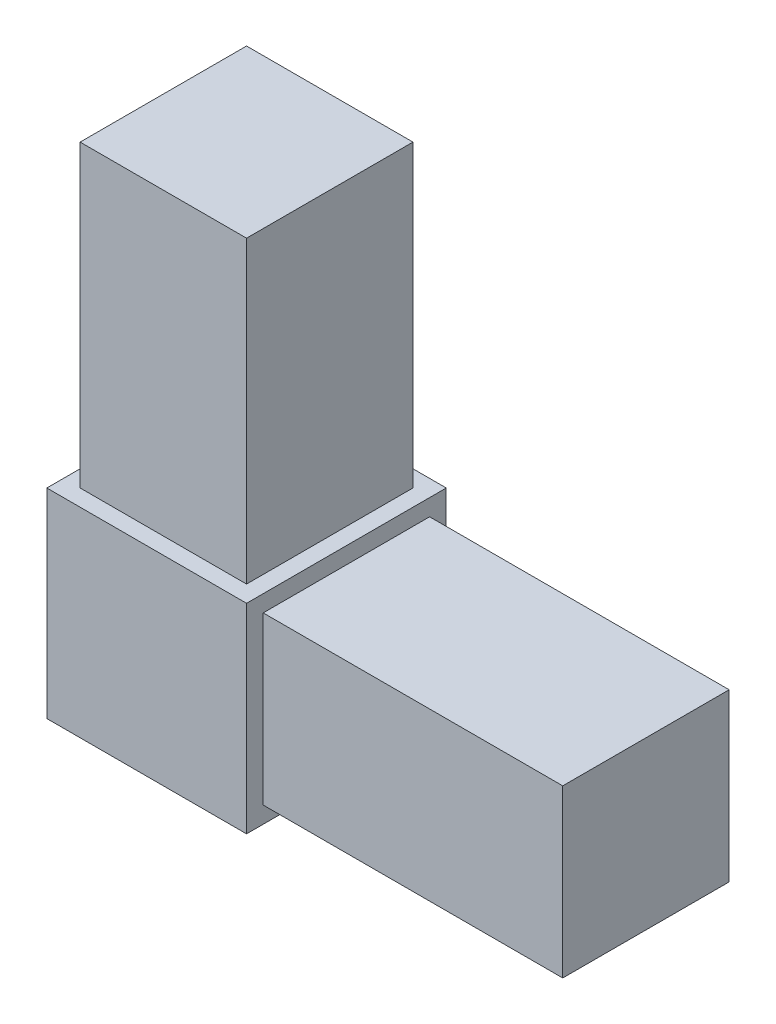
SolidWorks part; units mm, degrees
material "ABS"
ref_plane "Front Plane" through (0, 0, 0) normal (0, 0, 1) x (1, 0, 0)
ref_plane "Top Plane" through (0, 0, 0) normal (0, 1, 0) x (1, 0, 0)
ref_plane "Right Plane" through (0, 0, 0) normal (1, 0, 0) x (0, 0, -1)
sketch "Sketch1" plane through (0, 0, 0) normal (0, 0, 1) x (1, 0, 0)
  line L1 (9.525, -9.525) -> (-9.525, -9.525)
  line L2 (9.525, -9.525) -> (9.525, 9.525)
  line L3 (9.525, 9.525) -> (-9.525, 9.525)
  line L4 (-9.525, -9.525) -> (-9.525, 9.525)
  line L5 (9.525, -9.525) -> (-9.525, 9.525) construction
  line L6 (9.525, 9.525) -> (-9.525, -9.525) construction
  point P0 (0, 0)
  dimension "D1" = 19.05
extrude "Boss-Extrude1" add sketch "Sketch1" along normal blind 19.05
sketch "Sketch2" plane through (0, 9.525, 0) normal (0, 1, 0) x (1, 0, 0)
  line L0 (-9.525, 0) -> (9.525, -19.05) construction
  line L2 (-7.9375, -1.5875) -> (7.9375, -1.5875)
  line L3 (-7.9375, -1.5875) -> (-7.9375, -17.4625)
  line L4 (-7.9375, -17.4625) -> (7.9375, -17.4625)
  line L5 (7.9375, -1.5875) -> (7.9375, -17.4625)
  line L6 (-7.9375, -1.5875) -> (7.9375, -17.4625) construction
  line L7 (-7.9375, -17.4625) -> (7.9375, -1.5875) construction
  point P4 (0, -9.525)
  dimension "D1" = 15.875
extrude "Boss-Extrude2" add sketch "Sketch2" along normal blind 28.575
sketch "Sketch3" plane through (9.525, 0, 0) normal (1, 0, 0) x (0, 0, -1)
  line L0 (-19.05, 9.525) -> (0, -9.525) construction
  line L2 (-17.4625, -7.9375) -> (-1.5875, -7.9375)
  line L3 (-17.4625, -7.9375) -> (-17.4625, 7.9375)
  line L4 (-17.4625, 7.9375) -> (-1.5875, 7.9375)
  line L5 (-1.5875, -7.9375) -> (-1.5875, 7.9375)
  line L6 (-17.4625, -7.9375) -> (-1.5875, 7.9375) construction
  line L7 (-17.4625, 7.9375) -> (-1.5875, -7.9375) construction
  point P4 (-9.525, 0)
  dimension "D1" = 15.875
extrude "Boss-Extrude3" add sketch "Sketch3" along normal blind 28.575
equation "\"Height\"= 32in"
equation "\"Width\"= 23in"
equation "\"Depth\"= 20in"
equation "\"Plexi\"= .121in"
equation "\"MagnetThickness\"= .125in"
equation "\"MagnetDiameter\"= 12mm"
equation "\"DoorPlexi\" = \"Plexi\""
equation "\"BasePlateThickness\" = 0.5in"
equation "\"BasePlateWidth\" = \"Width\"+\"EBWidth\"-2*\"Plexi\""
equation "\"BasePlateDepth\" = \"TopBarDepth\"+2*\"CornerCube\""
equation "\"Boxsize\" = .75in"
equation "\"Boxinner\" = .625in"
equation "\"CornerCube\" = 0.75in"
equation "\"FingerLength\" = 1.125in"
equation "\"Cutwidth\"= .016in"
equation "\"Earsize\"= 1in + \"Cutwidth\" /2"
equation "\"Slotsize\" = 1in - \"CutWidth\" / 2"
equation "\"InnerWidth\" = \"Width\" - 2* \"Plexi\""
equation "\"InnerHeight\" = \"Height\" -2 * \"Plexi\""
equation "\"InnerDepth\" = \"Depth\" - 2*\"Plexi\""
equation "\"RearNumHoles\" = 4"
equation "\"RearHolesBorder\" = 2.25"
equation "\"RearHoleSpacing\" = (\"Width\" - 2*\"RearHolesBorder\") / (\"RearNumHoles\"-1)"
equation "\"RearBarLength\" = (\"InnerWidth\"-2*\"CornerCube\")"
equation "\"RearTopNumHoles\" = 4"
equation "\"RearTopHolesBorder\" = 3.1"
equation "\"RearTopHolesSpacing\" = (\"Width\" - 2*\"RearTopHolesBorder\") / (\"RearTopNumHoles\"-1)"
equation "\"SideTopNumHoles\" = 4"
equation "\"SideTopHoleOffset\"=\"CornerCube\"+\"FingerLength\"+\"Plexi\"+.5"
equation "\"SideTopHoleSpacing\" = (\"TopBarDepth\"-2*\"SideTopHoleOffset\") / (\"SideTopNumHoles\"-1)"
equation "\"SideHorizNumHoles\" = 4"
equation "\"SideHorizHoleBorder\" = 1.50"
equation "\"SideHorizHoleSpacing\" = (\"TopBarDepth\"-2*\"SideHorizHoleBorder\") / (\"SideHorizNumHoles\"-1)"
equation "\"SideVertBarLength\"=\"Height\"-\"BasePlateThickness\"-2*\"CornerCube\"-\"Plexi\""
equation "\"SideVertNumHoles\" = 4"
equation "\"SideVertHolesBorder\" = \"CornerCube\"+\"FingerLength\"+1.50"
equation "\"SideVertHoleSpacing\" = (\"InnerHeight\" - 2*\"SideVertHolesBorder\") / (\"SideVertNumHoles\"-1)"
equation "\"RearSideVertNumHoles\" = 4"
equation "\"RearSideVertHolesBorder\" = 2.4"
equation "\"RearSideVertHoleSpacing\" = (\"InnerHeight\" - 2*\"RearSideVertHolesBorder\") / (\"RearSideVertNumHoles\"-1)"
equation "\"RivetDia\" = .228in"
equation "\"SlotDepth\" = \"Plexi\" + 0.75in + .005in"
equation "\"SideSlotWidth\"   = \"Plexi\"+.005in"
equation "\"SidePanelVertSpacing\" = (\"Height\"-2*(1.75-\"Plexi\")) / 5"
equation "\"BottomPanelSideHoleSpacing\" = (\"InnerDepth\"-2*(1.75-\"Plexi\")) / 4"
equation "\"FrontDoorGap\" = .1in"
equation "\"TopDepth\" = \"Depth\"-\"DoorPlexi\"-\"FrontDoorGap\""
equation "\"TopBarDepth\" = \"Depth\"-\"DoorPlexi\"-\"Plexi\"-2*\"MagnetThickness\"-2*\"CornerCube\""
equation "\"D1@Boss-Extrude1\"=\"CornerCube\""
equation "\"D1@Sketch1\"=\"CornerCube\""
equation "\"D1@Boss-Extrude3\"=\"FingerLength\""
equation "\"D1@Boss-Extrude2\"=\"FingerLength\""
equation "\"FingerWidth\" = .625in"
equation "\"D1@Sketch3\"=\"FingerWidth\""
equation "\"D1@Sketch2\"=\"FingerWidth\""
